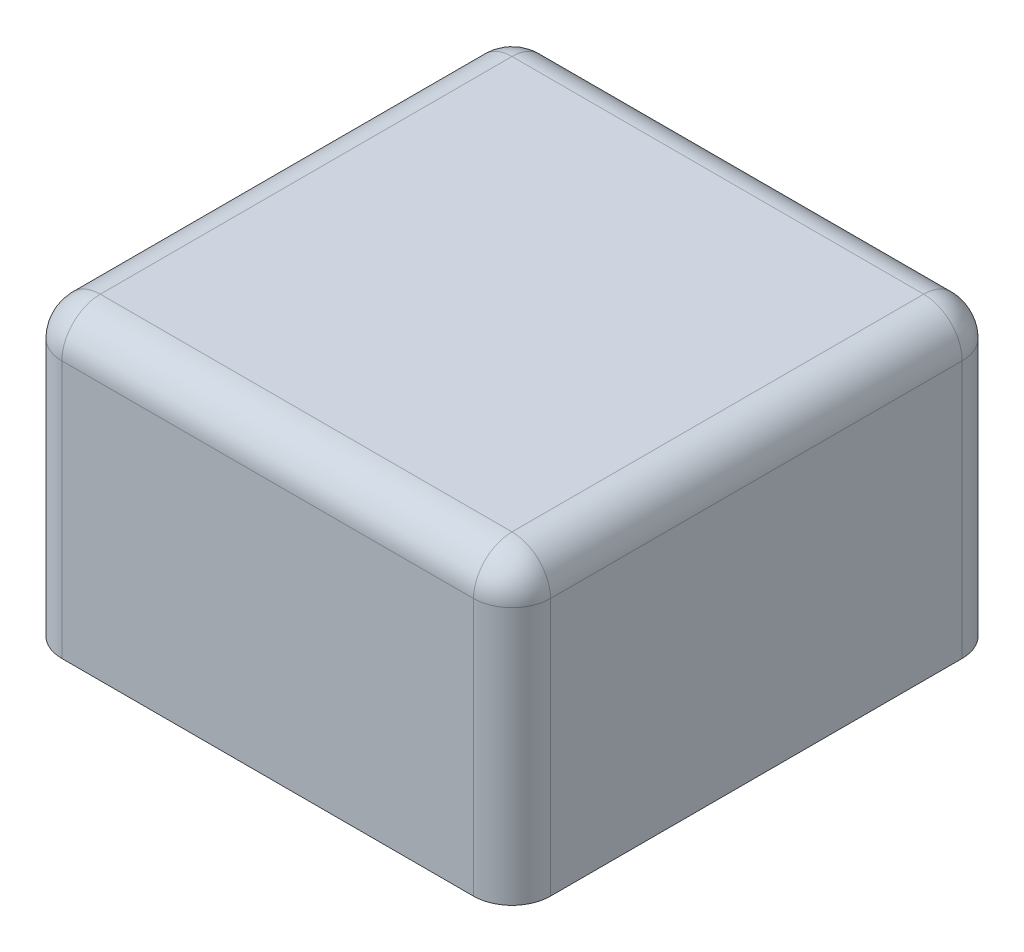
SolidWorks part; units mm, degrees
ref_plane "Front Plane" through (0, 0, 0) normal (0, 0, 1) x (1, 0, 0)
ref_plane "Top Plane" through (0, 0, 0) normal (0, 1, 0) x (1, 0, 0)
ref_plane "Right Plane" through (0, 0, 0) normal (1, 0, 0) x (0, 0, -1)
sketch "Sketch1" plane through (0, 0, 0) normal (0, 1, 0) x (1, 0, 0)
  line L1 (-12.7, -12.7) -> (12.7, -12.7)
  line L2 (-12.7, -12.7) -> (-12.7, 12.7)
  line L3 (-12.7, 12.7) -> (12.7, 12.7)
  line L4 (12.7, -12.7) -> (12.7, 12.7)
  line L5 (-12.7, -12.7) -> (12.7, 12.7) construction
  line L6 (-12.7, 12.7) -> (12.7, -12.7) construction
  point P0 (0, 0)
  dimension "D1" = 25.4
  dimension "D2" = 25.4
extrude "Boss-Extrude1" add sketch "Sketch1" along normal blind 15.4
fillet "Fillet1" radius 2 8 edges at (12.7, 7.7, -12.7) (12.7, 15.4, 0) (0, 15.4, -12.7) (-12.7, 7.7, -12.7) (12.7, 7.7, 12.7) (0, 15.4, 12.7) (-12.7, 7.7, 12.7) (-12.7, 15.4, 0)
